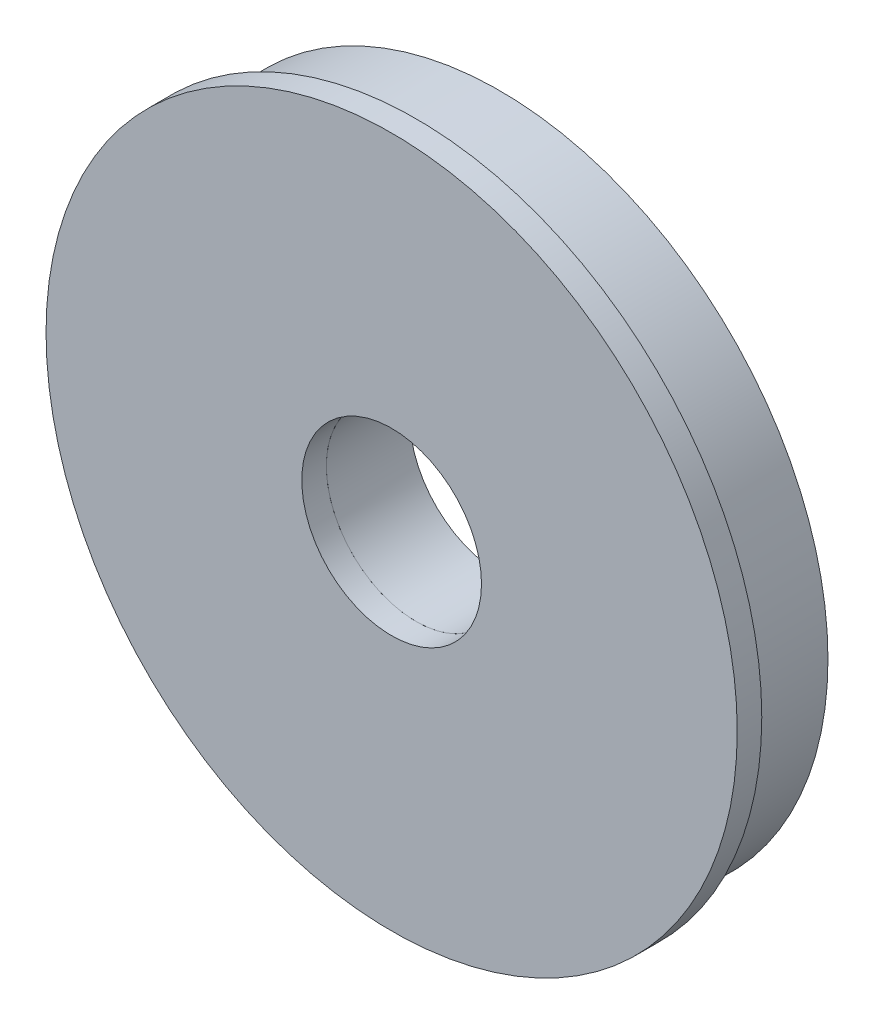
SolidWorks part; units mm, degrees
ref_plane "Front Plane" through (0, 0, 0) normal (0, 0, 1) x (1, 0, 0)
ref_plane "Top Plane" through (0, 0, 0) normal (0, 1, 0) x (1, 0, 0)
ref_plane "Right Plane" through (0, 0, 0) normal (1, 0, 0) x (0, 0, -1)
sketch "Sketch1" plane through (0, 0, 0) normal (0, 0, 1) x (1, 0, 0)
  circle A0 centre (0, 0) radius 3.302
  circle A1 centre (0, 0) radius 12.7
  dimension "ID" = 6.604
  dimension "OD" = 25.4
extrude "Extrude1" add sketch "Sketch1" against normal blind 0.9017
sketch "Sketch2" plane through (0, 0, -0.9017) normal (0, 0, -1) x (-1, 0, 0)
  circle A0 centre (0, 0) radius 3.302 construction
  circle A1 centre (0, 0) radius 3.302
  circle A2 centre (0, 0) radius 12.065
  dimension "D1" = 24.13
extrude "Extrude2" add sketch "Sketch2" along normal offset from surface (3.0671 mm away) 3.9688 separate body up to face at (3.302, 0, 0)
equation "\"D1@Sketch2\" = \"OD@Sketch1\"*.95"
